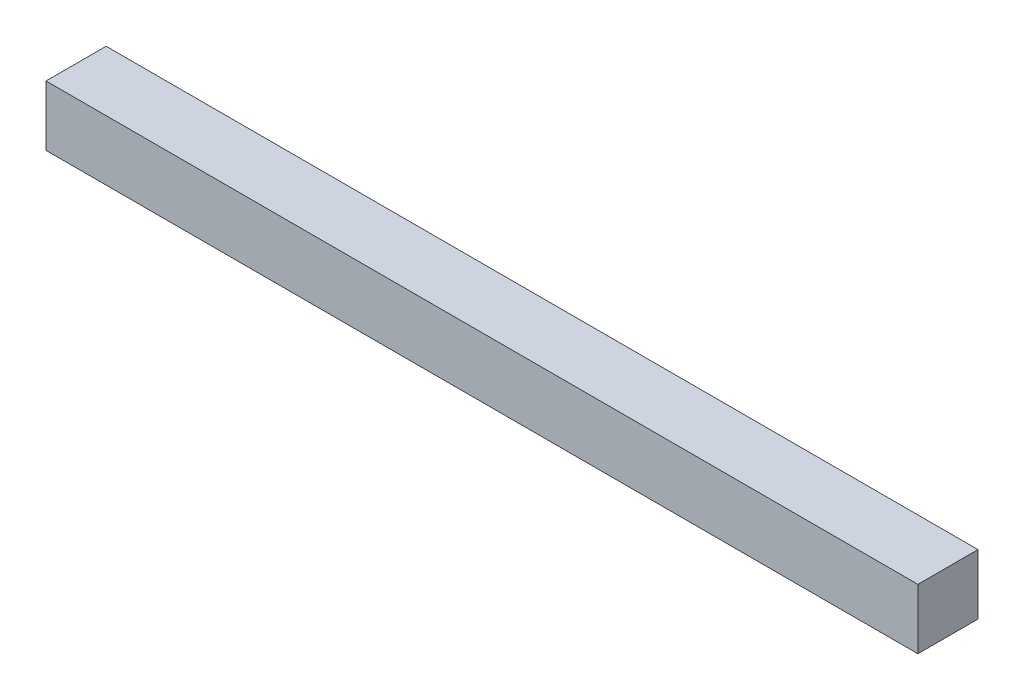
SolidWorks part; units mm, degrees
ref_plane "Front Plane" through (0, 0, 0) normal (0, 0, 1) x (1, 0, 0)
ref_plane "Top Plane" through (0, 0, 0) normal (0, 1, 0) x (1, 0, 0)
ref_plane "Right Plane" through (0, 0, 0) normal (1, 0, 0) x (0, 0, -1)
sketch "Sketch1" plane through (0, 0, 0) normal (0, 1, 0) x (1, 0, 0)
  line L1 (0, 0) -> (-46.035, 0)
  line L2 (0, 0) -> (0, 3.175)
  line L3 (0, 3.175) -> (-46.035, 3.175)
  line L4 (-46.035, 0) -> (-46.035, 3.175)
  dimension "D1" = 46.035
  dimension "D2" = 3.175
extrude "Boss-Extrude1" add sketch "Sketch1" along normal blind 3.175
